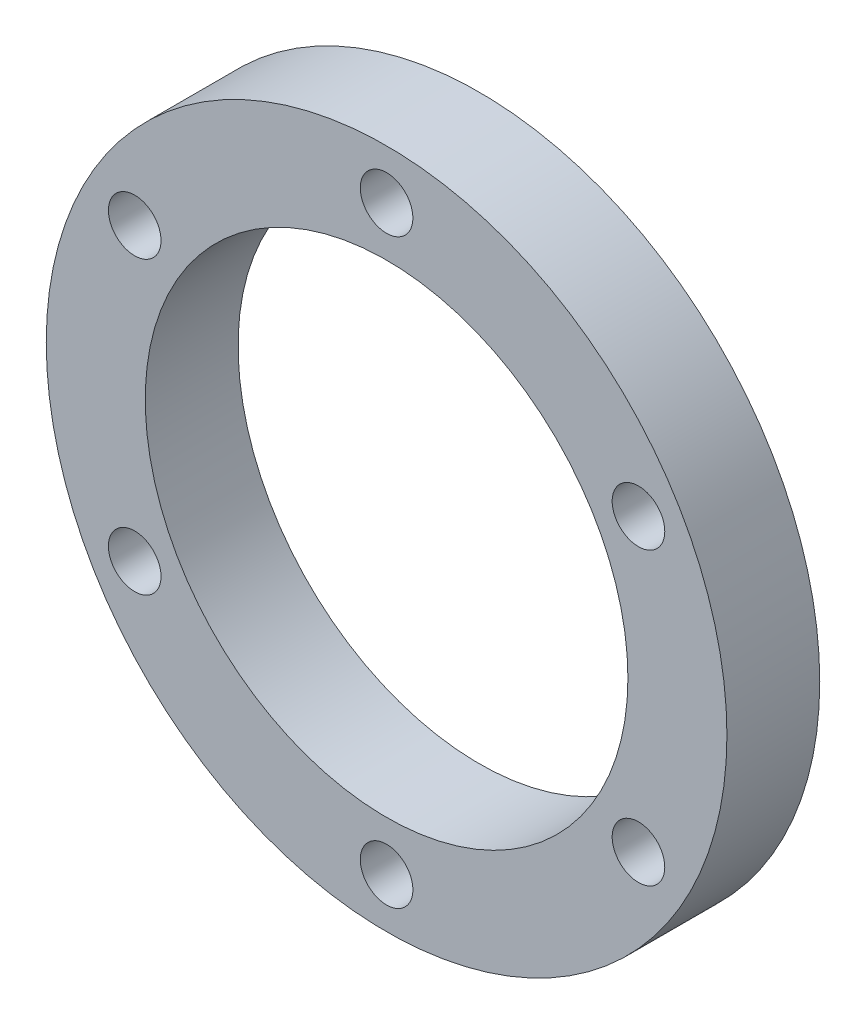
SolidWorks part; units mm, degrees
ref_plane "Plan de face" through (0, 0, 0) normal (0, 0, 1) x (1, 0, 0)
ref_plane "Plan de dessus" through (0, 0, 0) normal (0, 1, 0) x (1, 0, 0)
ref_plane "Plan de droite" through (0, 0, 0) normal (1, 0, 0) x (0, 0, -1)
sketch "Esquisse1" plane through (0, 0, 0) normal (0, 0, 1) x (1, 0, 0)
  circle A0 centre (0, 0) radius 55
  dimension "D1" = 110
extrude "Boss.-Extru.1" add sketch "Esquisse1" along normal blind 15
hole_wizard "Trou taraudé M101" positions "Esquisse3" profile "Esquisse2" tap size "M10" standard "ISO" end condition through all
sketch "Esquisse3" plane through (0, 0, 15) normal (0, 0, 1) x (1, 0, 0)
  circle A0 centre (0, 0) radius 47 construction
  point P0 (0, 47)
  dimension "D1" = 94
sketch "Esquisse2" plane through (0, 47, 15) normal (1, 0, 0) x (0, -1, 0)
  line L0 (0, 0) -> (0, 15)
  line L1 (0, 15) -> (4.25, 15)
  line L2 (4.25, 15) -> (4.25, 0)
  line L5 (4.25, 0) -> (0, 0)
  line L11 (0, -6.35) -> (0, 107.95) construction
  dimension "Diamètre du trou pour taraudage jusqu'au prochain" = 8.5
  dimension "Profondeur du trou pour taraudage jusqu'au prochain" = 15
cosmetic thread "Filetage de perçage1" parameters "D2"=10
pattern_circular "Répétition circulaire1" count 6 over 360 about axis through (0, 0, 0) along (0, 0, 1) of "Trou taraudé M101"
sketch "Esquisse4" plane through (0, 0, 15) normal (0, 0, 1) x (1, 0, 0)
  line L0 (0, 0) -> (0, 55) construction
  line L1 (0, 51.25) -> (-22.5328, 51.25) construction
  circle A0 centre (0, 0) radius 39
  circle A1 centre (40.7032, 23.5) radius 4.25 construction
  circle A2 centre (0, 0) radius 55 construction
  circle A3 centre (0, 47) radius 4.25 construction
  dimension "D1" = 78
  dimension "D2" = 3.75
  dimension "D3" = 3.75
extrude "Enlèv. mat.-Extru.1" cut sketch "Esquisse4" against normal through all
